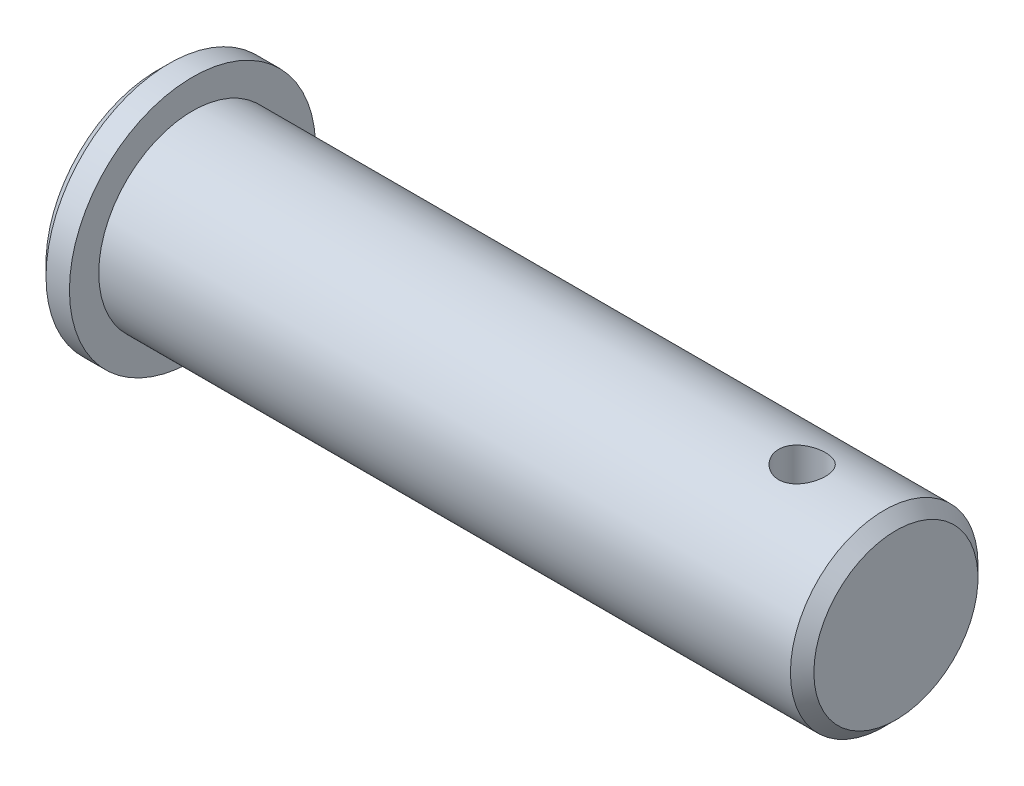
SolidWorks part; units mm, degrees
ref_plane "Płaszczyzna przednia" through (0, 0, 0) normal (0, 0, 1) x (1, 0, 0)
ref_plane "Płaszczyzna górna" through (0, 0, 0) normal (0, 1, 0) x (1, 0, 0)
ref_plane "Płaszczyzna prawa" through (0, 0, 0) normal (1, 0, 0) x (0, 0, -1)
sketch "Szkic1" plane through (0, 0, 0) normal (0, 0, 1) x (1, 0, 0)
  line L0 (0, 0) -> (0, 10.5)
  line L1 (0, 10.5) -> (3, 10.5)
  line L2 (3, 10.5) -> (3, 8)
  line L3 (3, 8) -> (63, 8)
  line L4 (0, 0) -> (63, 0)
  line L5 (63, 0) -> (63, 8)
  dimension "D1" = 10.5
  dimension "D2" = 8
  dimension "D3" = 3
  dimension "D4" = 60
revolve "Obrót1" add sketch "Szkic1" angle 360 about L4
chamfer "Sfazowanie2" distance 1 angle 45 2 edges at (63, 0, 8) (0, 0, 10.5)
sketch "Szkic2" plane through (0, 0, 0) normal (0, 1, 0) x (1, 0, 0)
  line L0 (0, 0) -> (55, 0) construction
  circle A0 centre (55, 0) radius 2
  dimension "D1" = 4
  dimension "D2" = 55
extrude "Wytnij-wyciągnięcie1" cut sketch "Szkic2" against normal through all and the other way through all
